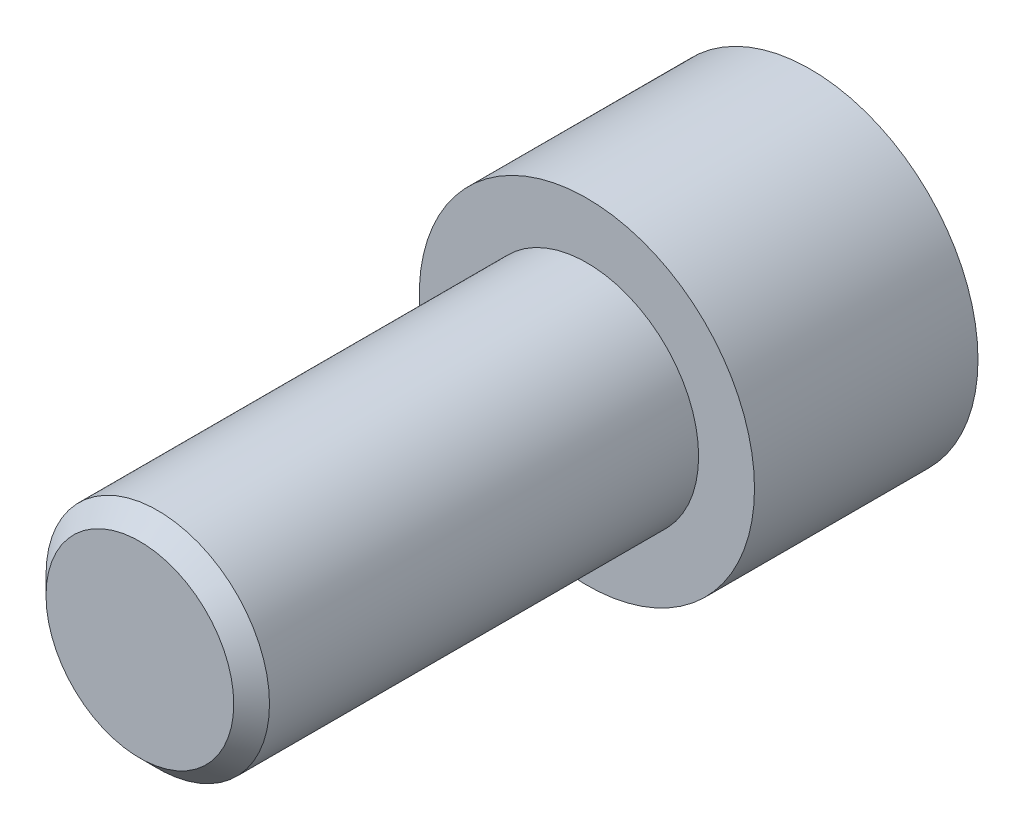
SolidWorks part; units mm, degrees
material "Plain Carbon Steel"
ref_plane "Front Plane" through (0, 0, 0) normal (0, 0, 1) x (1, 0, 0)
ref_plane "Top Plane" through (0, 0, 0) normal (0, 1, 0) x (1, 0, 0)
ref_plane "Right Plane" through (0, 0, 0) normal (1, 0, 0) x (0, 0, -1)
sketch "Sketch1" plane through (0, 0, 0) normal (0, 0, 1) x (1, 0, 0)
  circle A0 centre (0, 0) radius 4.7625
  dimension "D1" = 9.525
extrude "Boss-Extrude1" add sketch "Sketch1" against normal blind 6.35
sketch "Sketch2" plane through (0, 0, 0) normal (0, 0, 1) x (1, 0, 0)
  circle A0 centre (0, 0) radius 3.175
  dimension "D1" = 6.35
extrude "Boss-Extrude2" add sketch "Sketch2" along normal blind 12.7
chamfer "Chamfer1" distance 0.508 angle 45 1 edges at (3.175, 0, 12.7)
sketch "Sketch3" plane through (0, 0, -6.35) normal (0, 0, -1) x (-1, 0, 0)
  line L1 (0, 2.9329) -> (-2.54, 1.4665)
  line L2 (-2.54, 1.4665) -> (-2.54, -1.4665)
  line L3 (-2.54, -1.4665) -> (0, -2.9329)
  line L4 (0, -2.9329) -> (2.54, -1.4665)
  line L5 (2.54, -1.4665) -> (2.54, 1.4665)
  line L6 (2.54, 1.4665) -> (0, 2.9329)
  circle A0 centre (0, 0) radius 2.54 construction
  dimension "D1" = 5.08
extrude "Cut-Extrude1" cut sketch "Sketch3" against normal blind 3.81
